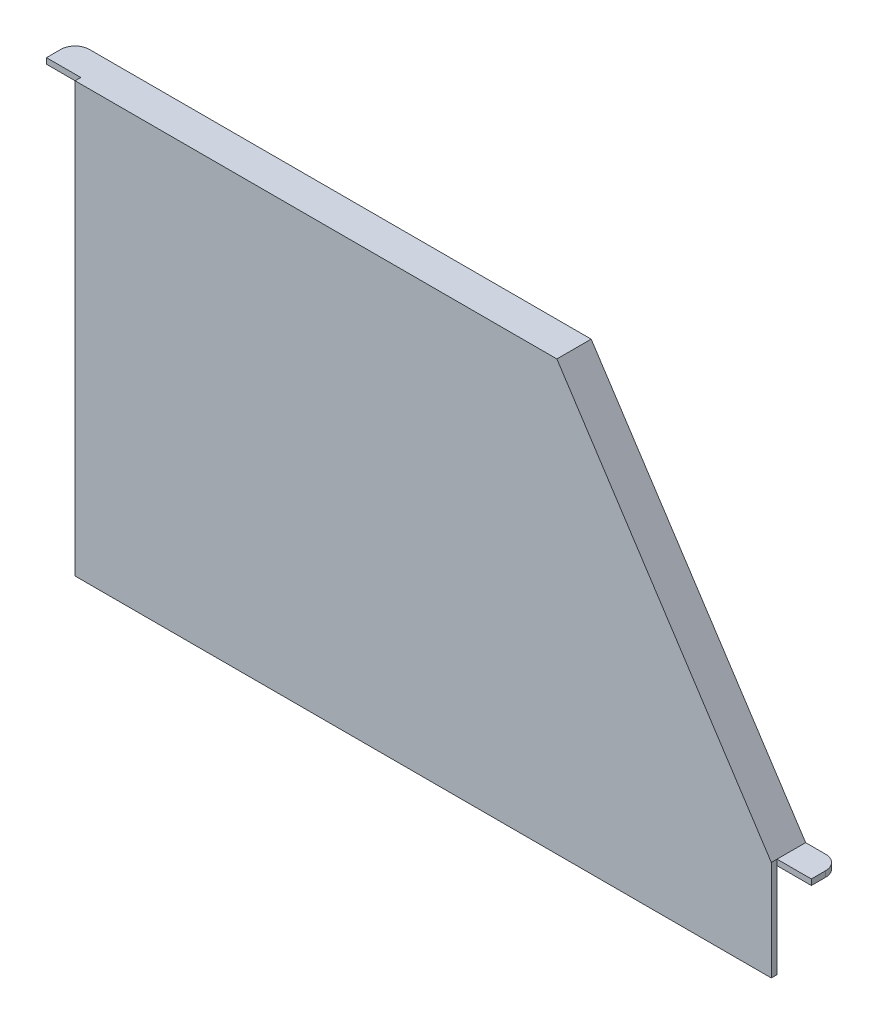
SolidWorks part; units mm, degrees
material "6061-T6 (SS)"
ref_plane "Front Plane" through (0, 0, 0) normal (0, 0, 1) x (1, 0, 0)
ref_plane "Top Plane" through (0, 0, 0) normal (0, 1, 0) x (1, 0, 0)
ref_plane "Right Plane" through (0, 0, 0) normal (1, 0, 0) x (0, 0, -1)
sketch "Sketch1" plane through (0, 0, 0) normal (0, 0, 1) x (1, 0, 0)
  line L0 (0, 0) -> (0, 300)
  line L1 (0, 300) -> (337, 300)
  line L2 (337, 300) -> (487, 70)
  line L3 (487, 70) -> (487, 0)
  line L4 (487, 0) -> (0, 0)
  dimension "D1" = 300
  dimension "D2" = 70
  dimension "D3" = 337
  dimension "D4" = 487
extrude "Boss-Extrude1" add sketch "Sketch1" along normal blind 4
sketch "Sketch2" plane through (0, 0, 0) normal (0, 0, -1) x (-1, 0, 0)
  line L1 (0, 300) -> (-337, 300)
  line L2 (0, 300) -> (0, 296)
  line L3 (0, 296) -> (-337, 296)
  line L4 (-337, 300) -> (-337, 296)
  dimension "D1" = 4
  dimension "D2" = 337
extrude "Boss-Extrude2" add sketch "Sketch2" along normal blind 20
sketch "Sketch3" plane through (0, 0, 0) normal (0, 0, -1) x (-1, 0, 0)
  line L8 (-337, 300) -> (-337, 296)
  line L9 (-337, 296) -> (-487, 66)
  line L10 (-487, 0) -> (-487, 70) construction
  line L11 (-487, 66) -> (-487, 70)
  line L12 (-487, 70) -> (-337, 300)
extrude "Boss-Extrude3" add sketch "Sketch3" along normal blind 20
sketch "Sketch7" plane through (487, 0, 0) normal (1, 0, 0) x (0, 0, -1)
  line L0 (0, 0) -> (0, 66) construction
  line L1 (20, 70) -> (0, 70)
  line L2 (20, 70) -> (20, 66)
  line L3 (20, 66) -> (0, 66)
  line L4 (0, 70) -> (0, 66)
  line L5 (20, 66) -> (0, 66) construction
extrude "Boss-Extrude6" add sketch "Sketch7" along normal blind 24
sketch "Sketch8" plane through (0, 0, 0) normal (-1, 0, 0) x (0, 0, 1)
  line L0 (4, 300) -> (-20, 300) construction
  line L1 (-20, 296) -> (0, 296)
  line L2 (-20, 296) -> (-20, 300)
  line L3 (-20, 300) -> (0, 300)
  line L4 (0, 296) -> (0, 300)
extrude "Boss-Extrude7" add sketch "Sketch8" along normal blind 24
fillet "Fillet1" radius 10 2 edges at (511, 68, -20) (-24, 298, -20)
